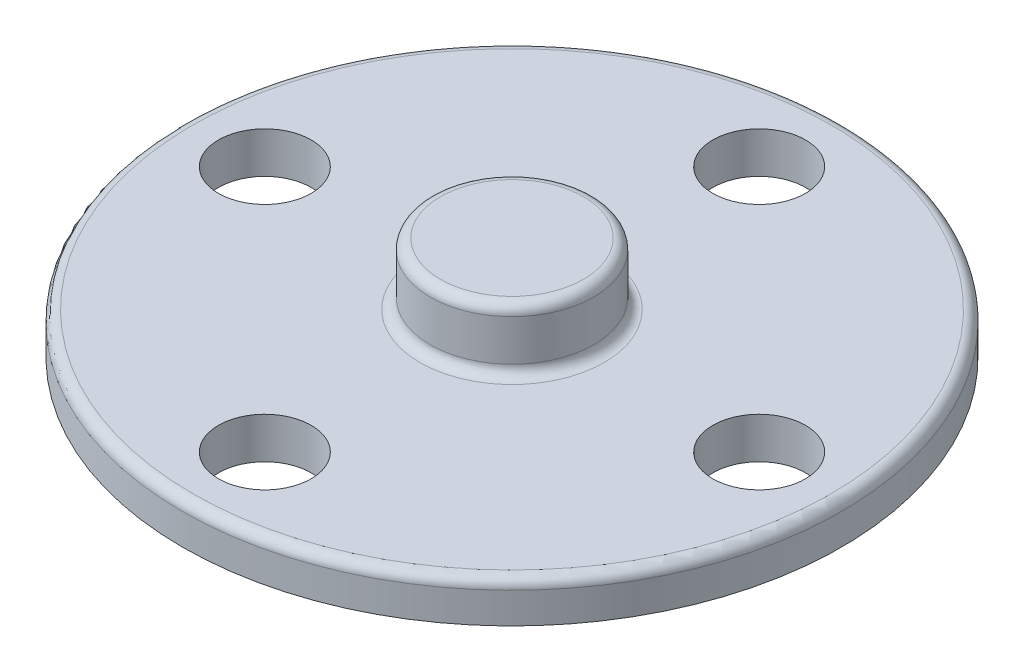
SolidWorks part; units mm, degrees
ref_plane "Front Plane" through (0, 0, 0) normal (0, 0, 1) x (1, 0, 0)
ref_plane "Top Plane" through (0, 0, 0) normal (0, 1, 0) x (1, 0, 0)
ref_plane "Right Plane" through (0, 0, 0) normal (1, 0, 0) x (0, 0, -1)
sketch "Sketch1" plane through (0, 0, 0) normal (0, 1, 0) x (1, 0, 0)
  circle A0 centre (0, 0) radius 16
  dimension "D1" = 32
extrude "Boss-Extrude1" add sketch "Sketch1" along normal blind 2
sketch "Sketch5" plane through (0, 2, 0) normal (0, 1, 0) x (1, 0, 0)
  circle A0 centre (0, 12) radius 2.25
  circle A1 centre (12, 0) radius 2.25
  circle A2 centre (0, -12) radius 2.25
  circle A3 centre (-12, 0) radius 2.25
  dimension "D1" = 4.5
  dimension "D2" = 12
  dimension "D3" = 4
extrude "Cut-Extrude1" cut sketch "Sketch5" against normal through all
sketch "Sketch6" plane through (0, 2, 0) normal (0, 1, 0) x (1, 0, 0)
  circle A0 centre (0, 0) radius 3.975
  dimension "D1" = 7.95
extrude "Boss-Extrude2" add sketch "Sketch6" along normal blind 3
fillet "Fillet1" radius 0.5 3 edges at (0, 2, 16) (0, 5, 3.975) (0, 2, 3.975)
